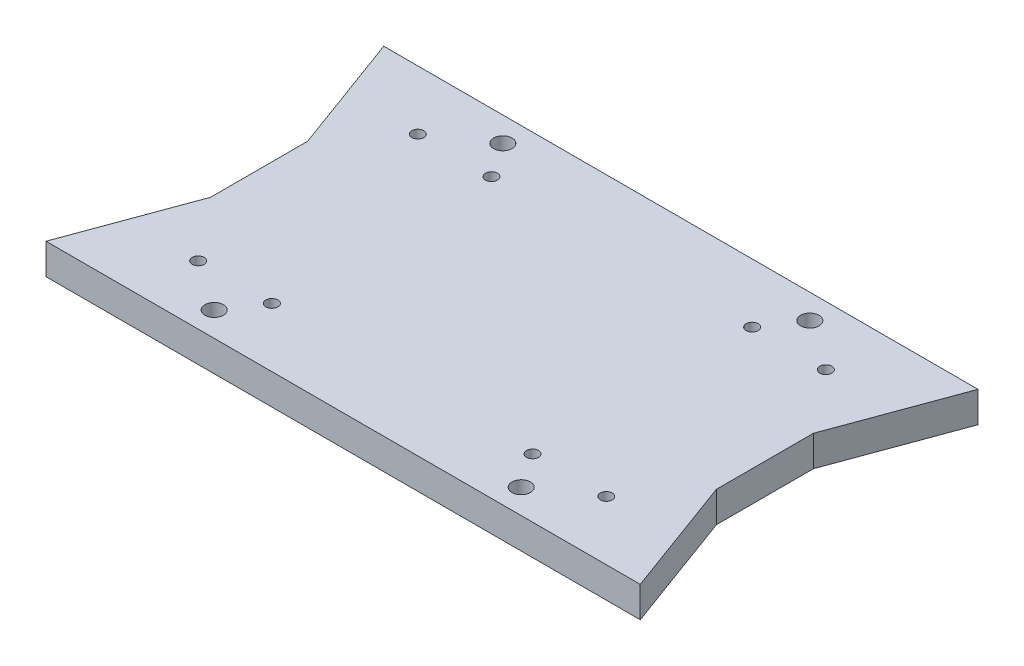
SolidWorks part; units mm, degrees
ref_plane "Front Plane" through (0, 0, 0) normal (0, 0, 1) x (1, 0, 0)
ref_plane "Top Plane" through (0, 0, 0) normal (0, 1, 0) x (1, 0, 0)
ref_plane "Right Plane" through (0, 0, 0) normal (1, 0, 0) x (0, 0, -1)
sketch "Sketch10" plane through (0, 0, 0) normal (0, 1, 0) x (1, 0, 0)
  line L0 (0, 69.85) -> (9.144, 44.958)
  line L1 (0, 0) -> (61.443, 0)
  line L3 (0, 69.85) -> (61.443, 69.85)
  line L5 (9.144, 44.958) -> (9.144, 24.895)
  line L6 (9.144, 24.895) -> (0, 0)
  line L8 (61.443, 0) -> (61.443, 69.85)
  circle A0 centre (29.693, 64.77) radius 1.905
  circle A1 centre (29.693, 5.08) radius 1.905
  point P6 (29.693, 64.77)
  point P11 (29.693, 5.08)
  dimension "D5" = 3.81
  dimension "D6" = 61.443
  dimension "D1" = 24.892
  dimension "D2" = 9.144
  dimension "D3" = 69.85
  dimension "D4" = 24.895
extrude "Boss-Extrude2" add sketch "Sketch10" along normal blind 6.35
sketch "Sketch11" plane through (0, 6.35, 0) normal (0, 1, 0) x (1, 0, 0)
  circle A0 centre (34.4903, 57.628) radius 1.2446
  circle A1 centre (19.2503, 57.628) radius 1.2446
  circle A2 centre (34.4903, 12.225) radius 1.2446
  circle A3 centre (19.2503, 12.225) radius 1.2446
  dimension "D1" = 2.4892
  dimension "D2" = 12.67
  dimension "D3" = 15.24
  dimension "D4" = 10.1063
  dimension "D5" = 12.67
  dimension "D6" = 10.1063
  dimension "D7" = 15.24
extrude "Cut-Extrude1" cut sketch "Sketch11" against normal blind 6.35
mirror "Mirror3" about plane through (61.443, 6.35, 0) normal (-1, 0, 0) of "Cut-Extrude1", "Boss-Extrude2"
